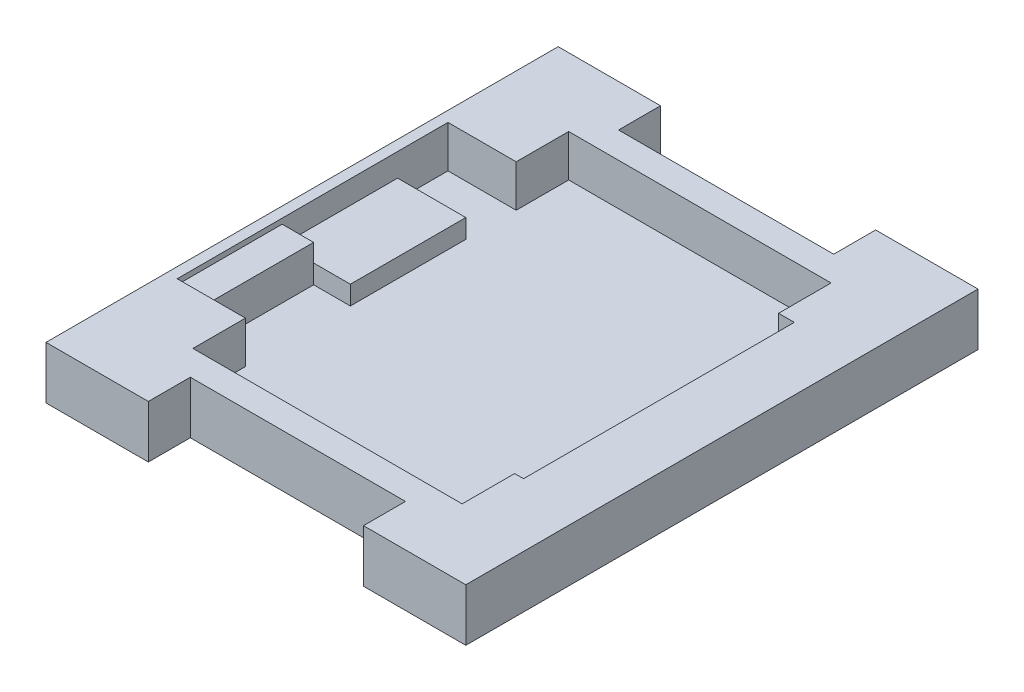
SolidWorks part; units mm, degrees
ref_plane "Front Plane" through (0, 0, 0) normal (0, 0, 1) x (1, 0, 0)
ref_plane "Top Plane" through (0, 0, 0) normal (0, 1, 0) x (1, 0, 0)
ref_plane "Right Plane" through (0, 0, 0) normal (1, 0, 0) x (0, 0, -1)
sketch "Sketch1" plane through (0, 0, 0) normal (0, 1, 0) x (1, 0, 0)
  line L1 (20, -24.4) -> (-20, -24.4)
  line L2 (20, -24.4) -> (20, 24.4)
  line L3 (20, 24.4) -> (-20, 24.4)
  line L4 (-20, -24.4) -> (-20, 24.4)
  line L5 (20, -24.4) -> (-20, 24.4) construction
  line L6 (20, 24.4) -> (-20, -24.4) construction
  point P0 (0, 0)
  dimension "D1" = 40
  dimension "D2" = 48.8
extrude "Boss-Extrude1" add sketch "Sketch1" along normal blind 1
sketch "Sketch2" plane through (0, 1, 0) normal (0, 1, 0) x (1, 0, 0)
  line L1 (19, -17.9) -> (-19, -17.9)
  line L2 (19, -17.9) -> (19, 17.9)
  line L3 (19, 17.9) -> (-19, 17.9)
  line L4 (-19, -17.9) -> (-19, 17.9)
  line L5 (19, -17.9) -> (-19, 17.9) construction
  line L6 (19, 17.9) -> (-19, -17.9) construction
  line L7 (20, -24.4) -> (-20, -24.4)
  line L8 (20, -24.4) -> (20, 24.4)
  line L9 (20, 24.4) -> (-20, 24.4)
  line L10 (-20, -24.4) -> (-20, 24.4)
  line L11 (20, -24.4) -> (-20, 24.4) construction
  line L12 (20, 24.4) -> (-20, -24.4) construction
  point P0 (0, 0)
  point P6 (0, 0)
  dimension "D1" = 38
  dimension "D2" = 35.8
extrude "Boss-Extrude2" add sketch "Sketch2" along normal blind 4
sketch "Sketch3" plane through (0, 5, 0) normal (0, 1, 0) x (1, 0, 0)
  line L0 (0, -24.4) -> (0, 24.4) construction
  line L1 (-20, -24.4) -> (20, -24.4) construction
  line L2 (20, 24.4) -> (-20, 24.4) construction
  line L4 (10.25, -28.4) -> (-10.25, -28.4)
  line L5 (10.25, -28.4) -> (10.25, -20.4)
  line L6 (10.25, -20.4) -> (-10.25, -20.4)
  line L7 (-10.25, -28.4) -> (-10.25, -20.4)
  line L8 (10.25, -28.4) -> (-10.25, -20.4) construction
  line L9 (10.25, -20.4) -> (-10.25, -28.4) construction
  line L10 (10.25, 28.4) -> (-10.25, 28.4)
  line L11 (10.25, 28.4) -> (10.25, 20.4)
  line L12 (10.25, 20.4) -> (-10.25, 20.4)
  line L13 (-10.25, 28.4) -> (-10.25, 20.4)
  line L14 (10.25, 28.4) -> (-10.25, 20.4) construction
  line L15 (10.25, 20.4) -> (-10.25, 28.4) construction
  dimension "D1" = 20.5
  dimension "D2" = 8
extrude "Cut-Extrude1" cut sketch "Sketch3" against normal through all
sketch "Sketch4" plane through (0, 5, 0) normal (0, 1, 0) x (1, 0, 0)
  line L1 (-19, -17.9) -> (-12.5, -17.9)
  line L2 (-19, -17.9) -> (-19, -12.9)
  line L3 (-19, -12.9) -> (-12.5, -12.9)
  line L4 (-12.5, -17.9) -> (-12.5, -12.9)
  line L5 (-19, 17.9) -> (-12.5, 17.9)
  line L6 (-19, 17.9) -> (-19, 12.9)
  line L7 (-19, 12.9) -> (-12.5, 12.9)
  line L8 (-12.5, 17.9) -> (-12.5, 12.9)
  line L9 (19, 17.9) -> (19, -17.9)
  line L10 (19, -17.9) -> (13.1508, -17.9)
  line L11 (-19, -17.9) -> (19, -17.9) construction
  line L12 (13.1508, -17.9) -> (13.1508, -12.9)
  line L13 (13.1508, -12.9) -> (14, -12.9)
  line L14 (14, -12.9) -> (14, 12.9)
  line L15 (14, 12.9) -> (12.5, 12.9)
  line L16 (12.5, 12.9) -> (12.5, 17.9)
  line L18 (19, 17.9) -> (-19, 17.9) construction
  line L19 (12.5, 17.9) -> (19, 17.9)
  dimension "D1" = 5
  dimension "D2" = 6.5
  dimension "D3" = 5
  dimension "D4" = 6.5
extrude "Boss-Extrude3" add sketch "Sketch4" against normal through all
sketch "Sketch5" plane through (0, 0, 0) normal (0, -1, 0) x (1, 0, 0)
  line L1 (-19.5, -8.1) -> (-12.5, -8.1)
  line L2 (-19.5, -8.1) -> (-19.5, 2.9)
  line L3 (-19.5, 2.9) -> (-12.5, 2.9)
  line L4 (-12.5, -8.1) -> (-12.5, 2.9)
  line L5 (-12.5, -12.9) -> (-12.5, -17.9) construction
  line L6 (-10.25, -24.4) -> (-20, -24.4) construction
  line L7 (-20, 24.4) -> (-10.25, 24.4) construction
  dimension "D1" = 7
  dimension "D2" = 16.3
  dimension "D3" = 21.5
extrude "Boss-Extrude4" add sketch "Sketch5" against normal blind 2.8
sketch "Sketch7" plane through (-20, 0, 0) normal (-1, 0, 0) x (0, 0, 1)
  line L0 (-24.4, 0) -> (24.4, 0) construction
  line L1 (12.9, 0) -> (2.9, 0)
  line L2 (12.9, 0) -> (12.9, 4.5)
  line L3 (12.9, 4.5) -> (2.9, 4.5)
  line L4 (2.9, 0) -> (2.9, 4.5)
  dimension "D1" = 4.5
extrude "Boss-Extrude5" add sketch "Sketch7" against normal blind 4
sketch3d "Sketch_MAC1-1_BOTTOM CASE_MILLING" [suppressed]
  line L0 (20, 0, 24.4) -> (20, 0, 14.4)
  line L1 (20, 0, 24.4) -> (10, 0, 24.4)
  point P0 (20, 0, 24.4)
  point P1 (20, 0, 14.4)
  point P2 (10, 0, 24.4)
sketch3d "Stock_BOTTOM CASE_MILLING"
  line L12 (20, 0, 24.4) -> (20, 0, -24.4)
  line L13 (20, 0, -24.4) -> (-20, 0, -24.4)
  line L14 (-20, 0, -24.4) -> (-20, 0, 24.4)
  line L15 (-20, 0, 24.4) -> (20, 0, 24.4)
  line L16 (20, 5, 24.4) -> (20, 5, -24.4)
  line L17 (20, 5, -24.4) -> (-20, 5, -24.4)
  line L18 (-20, 5, -24.4) -> (-20, 5, 24.4)
  line L19 (-20, 5, 24.4) -> (20, 5, 24.4)
  line L20 (20, 0, 24.4) -> (20, 5, 24.4)
  line L21 (20, 0, -24.4) -> (20, 5, -24.4)
  line L22 (-20, 0, -24.4) -> (-20, 5, -24.4)
  line L23 (-20, 0, 24.4) -> (-20, 5, 24.4)
  point P36 (20, 0, 0)
  point P37 (0, 0, -24.4)
  point P38 (-20, 0, 0)
  point P39 (0, 0, 24.4)
  point P40 (20, 5, 0)
  point P41 (0, 5, -24.4)
  point P42 (-20, 5, 0)
  point P43 (0, 5, 24.4)
  point P44 (20, 2.5, 24.4)
  point P45 (20, 2.5, -24.4)
  point P46 (-20, 2.5, -24.4)
  point P47 (-20, 2.5, 24.4)
  point P48 (0, 2.5, 0)
  point P49 (20, 2.5, 0)
  point P50 (0, 5, 0)
  point P51 (-20, 2.5, 0)
  point P52 (0, 0, 0)
  point P53 (0, 2.5, 24.4)
  point P54 (0, 2.5, -24.4)
